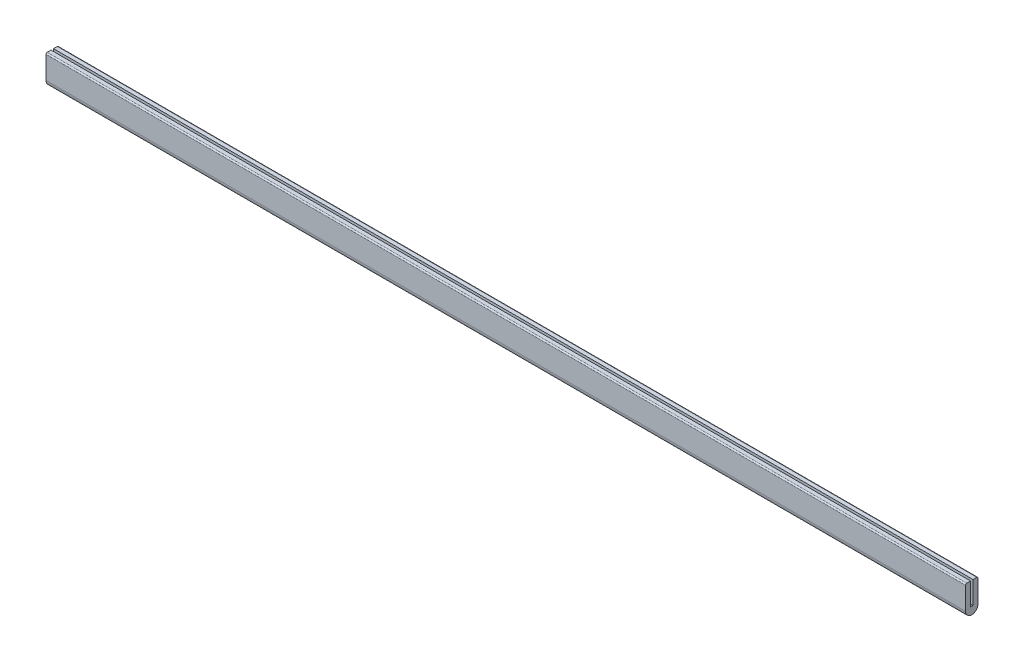
SolidWorks part; units mm, degrees
material "Rubber"
ref_plane "Front Plane" through (0, 0, 0) normal (0, 0, 1) x (1, 0, 0)
ref_plane "Top Plane" through (0, 0, 0) normal (0, 1, 0) x (1, 0, 0)
ref_plane "Right Plane" through (0, 0, 0) normal (1, 0, 0) x (0, 0, -1)
sketch "Sketch1" plane through (0, 0, 0) normal (1, 0, 0) x (0, 0, -1)
  line L0 (-1.5875, 28.575) -> (-7.9375, 28.575)
  line L1 (-1.5875, 28.575) -> (1.5875, 28.575) construction
  line L2 (-1.5875, 28.575) -> (-1.5875, 0)
  line L3 (-1.5875, 0) -> (1.5875, 0)
  line L4 (1.5875, 28.575) -> (1.5875, 0)
  line L5 (-7.9375, 28.575) -> (7.9375, 28.575) construction
  line L6 (-7.9375, 28.575) -> (-7.9375, -1.5875)
  line L8 (7.9375, 28.575) -> (7.9375, -1.5875)
  line L9 (7.9375, 28.575) -> (1.5875, 28.575)
  arc A0 (7.9375, -1.5875) -> (-7.9375, -1.5875) centre (0, -1.5875) cw
  point P4 (0, 0)
  point P10 (0, 28.575)
  point P12 (0, -9.525)
  dimension "D1" = 3.175
  dimension "D2" = 28.575
  dimension "D3" = 38.1
  dimension "D4" = 6.35
extrude "Boss-Extrude1" add sketch "Sketch1" along normal mid plane 1168.4
fillet "Fillet1" radius 1.5875 2 edges at (0, 28.575, 7.9375) (0, 28.575, -7.9375)
